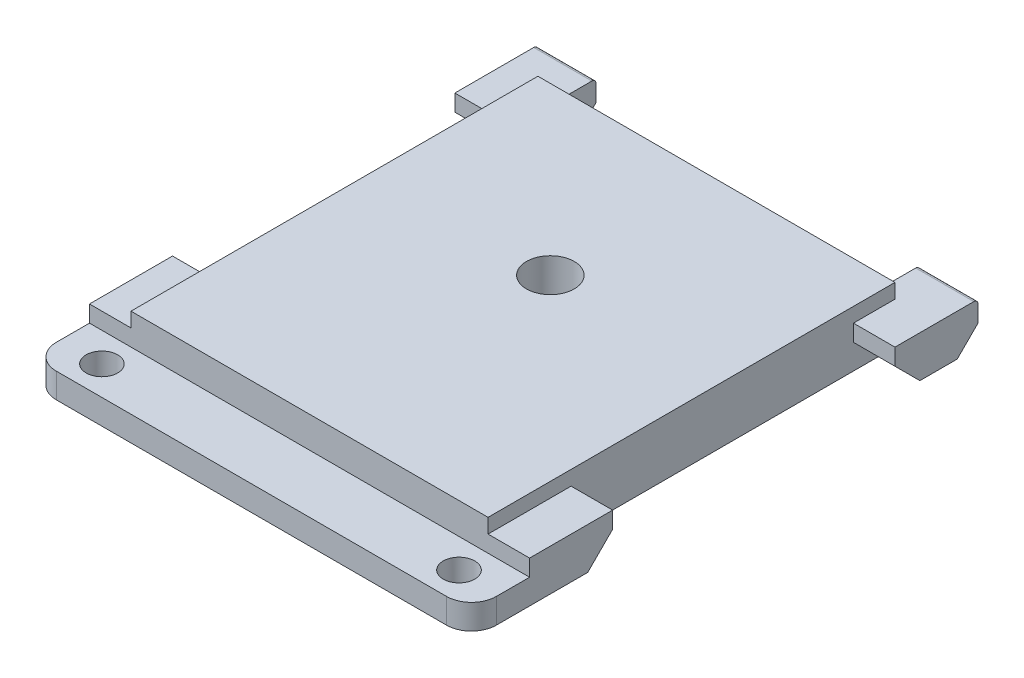
SolidWorks part; units mm, degrees
ref_plane "Front Plane" through (0, 0, 0) normal (0, 0, 1) x (1, 0, 0)
ref_plane "Top Plane" through (0, 0, 0) normal (0, 1, 0) x (1, 0, 0)
ref_plane "Right Plane" through (0, 0, 0) normal (1, 0, 0) x (0, 0, -1)
sketch "Sketch1" plane through (0, 0, 0) normal (0, 1, 0) x (1, 0, 0)
  line L0 (21.5, 0) -> (21.5, -20)
  line L1 (0, 0) -> (43, 0)
  line L2 (0, 0) -> (0, -49)
  line L3 (0, -49) -> (43, -49)
  line L4 (43, 0) -> (43, -49)
  circle A0 centre (21.5, -20) radius 2.875
  dimension "D3" = 20
  dimension "D4" = 5.75
  dimension "D1" = 43
  dimension "D2" = 49
extrude "Boss-Extrude1" add sketch "Sketch1" along normal blind 6.75
sketch "Sketch2" plane through (0, 0, 0) normal (-1, 0, 0) x (0, 0, 1)
  line L0 (49, 6.75) -> (49, 0) construction
  line L1 (0, 0) -> (49, 0)
  line L2 (0, 0) -> (0, 5)
  line L3 (0, 5) -> (49, 5)
  line L4 (49, 0) -> (49, 5)
  dimension "D1" = 5
extrude "Boss-Extrude2" add sketch "Sketch2" along normal blind 5
sketch "Sketch3" plane through (43, 0, 0) normal (1, 0, 0) x (0, 0, -1)
  line L0 (0, 6.75) -> (0, 0) construction
  line L1 (-49, 0) -> (0, 0)
  line L2 (-49, 0) -> (-49, 5)
  line L3 (-49, 5) -> (0, 5)
  line L4 (0, 0) -> (0, 5)
  dimension "D1" = 5
extrude "Boss-Extrude3" add sketch "Sketch3" along normal blind 5
sketch "Sketch4" plane through (0, 0, 0) normal (0, 0, -1) x (-1, 0, 0)
  line L0 (5, 0) -> (-48, 0) construction
  line L1 (-48, 5) -> (-41, 5)
  line L2 (-48, 5) -> (-48, 0)
  line L3 (-48, 0) -> (-41, 0)
  line L4 (-41, 5) -> (-41, 0)
  line L6 (5, 0) -> (-2, 0)
  line L7 (5, 0) -> (5, 5)
  line L8 (5, 5) -> (-2, 5)
  line L9 (-2, 0) -> (-2, 5)
  dimension "D1" = 7
  dimension "D2" = 7
extrude "Boss-Extrude4" add sketch "Sketch4" along normal blind 5
chamfer "Chamfer1" distance 2.5 angle 45 2 edges at (-1.5, 0, -5) (44.5, 0, -5)
fillet "Fillet1" radius 0.5 2 edges at (-1.5, 5, -5) (44.5, 5, -5)
sketch "Sketch6" plane through (0, 0, 49) normal (0, 0, 1) x (1, 0, 0)
  line L0 (48, 5) -> (48, 0) construction
  line L1 (-5, 0) -> (48, 0)
  line L2 (-5, 0) -> (-5, 3)
  line L3 (-5, 3) -> (48, 3)
  line L4 (48, 0) -> (48, 3)
  dimension "D1" = 3
extrude "Boss-Extrude6" add sketch "Sketch6" along normal blind 7
sketch "Sketch7" plane through (0, 3, 0) normal (0, 1, 0) x (1, 0, 0)
  circle A0 centre (0, -52.5) radius 1.9
  circle A1 centre (43, -52.5) radius 1.9
extrude "Cut-Extrude1" cut sketch "Sketch7" against normal up to surface (3 mm away)
sketch "Sketch9" plane through (-5, 0, 0) normal (-1, 0, 0) x (0, 0, 1)
  line L3 (49, 5) -> (-4.5, 5) construction
  line L4 (-2.5, 0) -> (56, 0) construction
  line L5 (5, 5) -> (39, 5)
  line L6 (5, 5) -> (5, 0)
  line L7 (5, 0) -> (39, 0)
  line L8 (39, 5) -> (39, 0)
extrude "Cut-Extrude2" cut sketch "Sketch9" against normal up to surface (5 mm away) up to face at (0, 5.875, 24.5)
sketch "Sketch10" plane through (48, 0, 0) normal (1, 0, 0) x (0, 0, -1)
  line L2 (-5, 2.5) -> (-5, 5)
  line L3 (4.5, 5) -> (-49, 5) construction
  line L4 (-56, 0) -> (2.5, 0) construction
  line L5 (-5, 5) -> (-39, 5)
  line L6 (-5, 5) -> (-5, 0)
  line L7 (-5, 0) -> (-39, 0)
  line L8 (-39, 5) -> (-39, 0)
extrude "Cut-Extrude3" cut sketch "Sketch10" against normal up to surface (5 mm away) contours L6 L5 L8 L7 up to face at (43, 5.875, 24.5)
chamfer "Chamfer2" distance 3 angle 45 4 edges at (-2.5, 0, 39) (-2.5, 0, 5) (45.5, 0, 5) (45.5, 0, 39)
fillet "Fillet2" radius 3 2 edges at (48, 1.5, 56) (-5, 1.5, 56)
